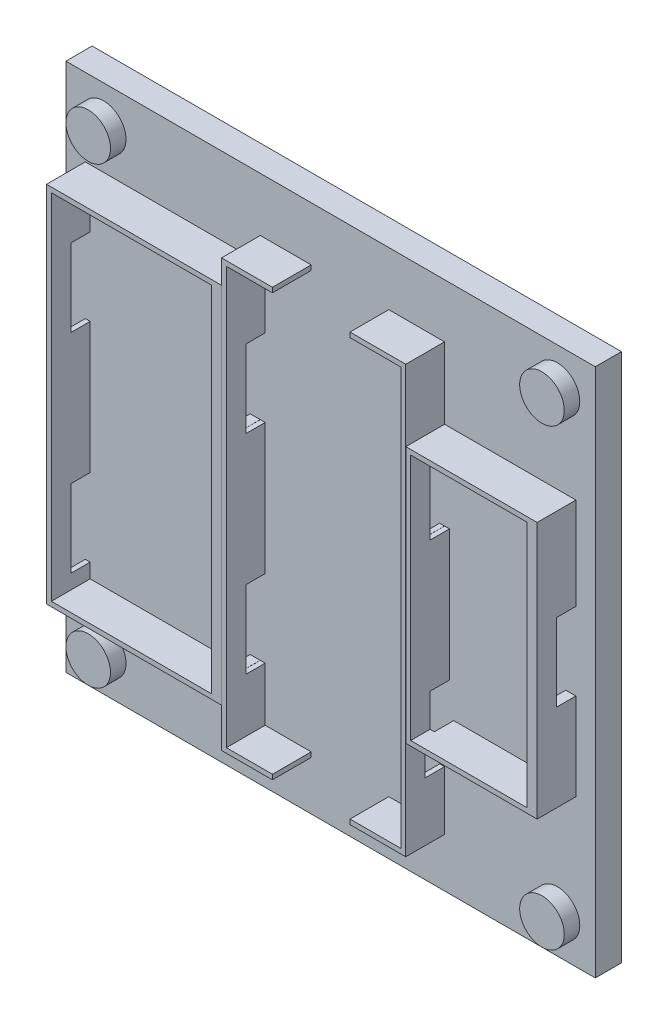
SolidWorks part; units mm, degrees
ref_plane "Přední rovina" through (0, 0, 0) normal (0, 0, 1) x (1, 0, 0)
ref_plane "Horní rovina" through (0, 0, 0) normal (0, 1, 0) x (1, 0, 0)
ref_plane "Pravá rovina" through (0, 0, 0) normal (1, 0, 0) x (0, 0, -1)
sketch "Skica1" plane through (0, 0, 0) normal (0, 0, 1) x (1, 0, 0)
  line L1 (-27.3, 27.3) -> (27.3, 27.3)
  line L2 (-27.3, 27.3) -> (-27.3, -27.3)
  line L3 (-27.3, -27.3) -> (27.3, -27.3)
  line L4 (27.3, 27.3) -> (27.3, -27.3)
  line L5 (-27.3, 27.3) -> (27.3, -27.3) construction
  line L6 (-27.3, -27.3) -> (27.3, 27.3) construction
  circle A0 centre (-23.4, 23.4) radius 2.3
  circle A1 centre (23.4, 23.4) radius 2.3
  circle A2 centre (-23.4, -23.4) radius 2.3
  circle A3 centre (23.4, -23.4) radius 2.3
  point P0 (0, 0)
  dimension "D2" = 4.6
  dimension "D6" = 4.6
  dimension "D9" = 4.6
  dimension "D11" = 4.6
  dimension "D1" = 54.6
  dimension "D3" = 3.9
  dimension "D4" = 3.9
  dimension "D5" = 5.5154
  dimension "D7" = 3.9
  dimension "D8" = 3.9
  dimension "D10" = 3.9
extrude "Přidat vysunutím1" add sketch "Skica1" along normal blind 1.7
sketch "Skica2" plane through (0, 0, 1.7) normal (0, 0, 1) x (1, 0, 0)
  line L1 (-27.3, 27.3) -> (27.3, 27.3)
  line L2 (-27.3, 27.3) -> (-27.3, -27.3)
  line L3 (-27.3, -27.3) -> (27.3, -27.3)
  line L4 (27.3, 27.3) -> (27.3, -27.3)
  line L5 (-27.3, 27.3) -> (27.3, -27.3) construction
  line L6 (-27.3, -27.3) -> (27.3, 27.3) construction
  point P0 (0, 0)
  dimension "D1" = 54.6
extrude "Přidat vysunutím2" add sketch "Skica2" along normal blind 1
sketch "Skica3" plane through (0, 0, 2.7) normal (0, 0, 1) x (1, 0, 0)
  line L0 (-27.3, 27.3) -> (-27.3, -27.3) construction
  line L1 (27.3, 27.3) -> (-27.3, 27.3) construction
  line L2 (27.3, -27.3) -> (27.3, 27.3) construction
  line L3 (-27.3, -27.3) -> (27.3, -27.3) construction
  circle A0 centre (-23.4, 23.4) radius 2.3
  circle A1 centre (23.4, 23.4) radius 2.3
  circle A2 centre (-23.4, -23.4) radius 2.3
  circle A3 centre (23.4, -23.4) radius 2.3
  dimension "D1" = 4.6
  dimension "D4" = 4.6
  dimension "D6" = 4.6
  dimension "D8" = 4.6
  dimension "D2" = 3.9
  dimension "D3" = 3.9
  dimension "D5" = 3.9
  dimension "D7" = 3.9
extrude "Přidat vysunutím3" add sketch "Skica3" along normal blind 1.6
sketch "Skica4" plane through (0, 0, 2.7) normal (0, 0, 1) x (1, 0, 0)
  line L0 (27.3, -27.3) -> (27.3, 27.3) construction
  line L1 (25.3, 14.3927) -> (11.76, 14.3927)
  line L2 (25.3, 14.3927) -> (25.3, -12.1073)
  line L3 (25.3, -12.1073) -> (11.76, -12.1073)
  line L4 (11.76, 14.3927) -> (11.76, -12.1073)
  line L5 (25.3, 14.3927) -> (11.76, -12.1073) construction
  line L6 (25.3, -12.1073) -> (11.76, 14.3927) construction
  line L7 (-27.3, 27.3) -> (-27.3, -27.3) construction
  line L8 (11.75, 21.75) -> (-7.25, 21.75)
  line L9 (11.75, 21.75) -> (11.75, -22.25)
  line L10 (11.75, -22.25) -> (-7.25, -22.25)
  line L11 (-7.25, 21.75) -> (-7.25, -22.25)
  line L12 (11.75, 21.75) -> (-7.25, -22.25) construction
  line L13 (11.75, -22.25) -> (-7.25, 21.75) construction
  line L14 (-7.26, 19.3) -> (-25.3, 19.3)
  line L15 (-7.26, 19.3) -> (-7.26, -18.2)
  line L16 (-7.26, -18.2) -> (-25.3, -18.2)
  line L17 (-25.3, 19.3) -> (-25.3, -18.2)
  line L18 (-7.26, 19.3) -> (-25.3, -18.2) construction
  line L19 (-7.26, -18.2) -> (-25.3, 19.3) construction
  line L20 (27.3, 27.3) -> (-27.3, 27.3) construction
  point P0 (18.53, 1.1427)
  point P7 (0, 0)
  point P12 (-16.28, 0.55)
  point P18 (0, 0)
  dimension "D1" = 26.5
  dimension "D2" = 13.54
  dimension "D3" = 2
  dimension "D4" = 44
  dimension "D5" = 19
  dimension "D6" = 37.5
  dimension "D7" = 18.04
  dimension "D8" = 0.01
  dimension "D9" = 2
  dimension "D10" = 0.01
  dimension "D11" = 8
extrude "Přidat vysunutím4" add sketch "Skica4" along normal blind 4
sketch "Skica5" plane through (0, -22.25, 0) normal (0, -1, 0) x (-1, 0, 0)
  line L0 (7.25, -6.7) -> (-11.75, -6.7) construction
  line L1 (-6, -6.7) -> (2, -6.7)
  line L2 (-6, -6.7) -> (-6, -2.7)
  line L3 (-6, -2.7) -> (2, -2.7)
  line L4 (2, -6.7) -> (2, -2.7)
  line L5 (27.3, -2.7) -> (-27.3, -2.7) construction
  line L8 (7.25, -6.7) -> (7.25, -2.7) construction
  line L9 (-11.75, -6.7) -> (-11.75, -2.7) construction
  dimension "D1" = 8
  dimension "D2" = 5.25
  dimension "D3" = 5.75
extrude "Odebrat vysunutím1" cut sketch "Skica5" against normal blind 6
sketch "Skica6" plane through (0, 21.75, 0) normal (0, 1, 0) x (1, 0, 0)
  line L0 (11.75, -6.7) -> (-7.25, -6.7) construction
  line L1 (-2, -2.7) -> (6, -2.7)
  line L2 (-2, -2.7) -> (-2, -6.7)
  line L3 (-2, -6.7) -> (6, -6.7)
  line L4 (6, -2.7) -> (6, -6.7)
  line L5 (-2, -2.7) -> (6, -6.7) construction
  line L6 (-2, -6.7) -> (6, -2.7) construction
  line L7 (-7.25, -6.7) -> (-7.25, -2.7) construction
  point P0 (2, -4.7)
  dimension "D1" = 4
  dimension "D2" = 8
  dimension "D3" = 0
  dimension "D4" = 5.25
extrude "Odebrat vysunutím2" cut sketch "Skica6" against normal blind 6
sketch "Skica7" plane through (-25.3, 0, 0) normal (-1, 0, 0) x (0, 0, 1)
  line L0 (2.7, -27.3) -> (2.7, 27.3) construction
  line L1 (2.7, -16.2) -> (4.7, -16.2)
  line L2 (2.7, -16.2) -> (2.7, -8.2)
  line L3 (2.7, -8.2) -> (4.7, -8.2)
  line L4 (4.7, -16.2) -> (4.7, -8.2)
  line L5 (2.7, -16.2) -> (4.7, -8.2) construction
  line L6 (2.7, -8.2) -> (4.7, -16.2) construction
  line L7 (6.7, -18.2) -> (2.7, -18.2) construction
  line L8 (2.7, 19.3) -> (2.7, -18.2) construction
  line L9 (2.7, 13.3) -> (4.7, 13.3)
  line L10 (2.7, 13.3) -> (2.7, 5.3)
  line L11 (2.7, 5.3) -> (4.7, 5.3)
  line L12 (4.7, 13.3) -> (4.7, 5.3)
  line L13 (6.7, 19.3) -> (2.7, 19.3) construction
  point P0 (3.7, -12.2)
  dimension "D1" = 8
  dimension "D2" = 2
  dimension "D3" = 0
  dimension "D4" = 2
  dimension "D5" = 8
  dimension "D6" = 2
  dimension "D7" = 6
extrude "Odebrat vysunutím3" cut sketch "Skica7" against normal blind 38
sketch "Skica8" plane through (25.3, 0, 0) normal (1, 0, 0) x (0, 0, -1)
  line L0 (-2.7, -12.1073) -> (-2.7, 14.3927) construction
  line L1 (-2.7, -3.1073) -> (-4.7, -3.1073)
  line L2 (-2.7, -3.1073) -> (-2.7, 4.8927)
  line L3 (-2.7, 4.8927) -> (-4.7, 4.8927)
  line L4 (-4.7, -3.1073) -> (-4.7, 4.8927)
  line L6 (-6.7, -12.1073) -> (-2.7, -12.1073) construction
  line L7 (-6.7, 14.3927) -> (-2.7, 14.3927) construction
  dimension "D1" = 8
  dimension "D2" = 2
  dimension "D3" = 9
  dimension "D4" = 9.5
extrude "Odebrat vysunutím4" cut sketch "Skica8" against normal blind 13
sketch "Skica11" plane through (0, 0, 6.7) normal (0, 0, 1) x (1, 0, 0)
  line L0 (-7.26, 19.3) -> (-25.3, 19.3) construction
  line L1 (-24.8, 18.8) -> (-8.3, 18.8)
  line L2 (-24.8, 18.8) -> (-24.8, -17.7)
  line L3 (-24.8, -17.7) -> (-8.3, -17.7)
  line L4 (-8.3, 18.8) -> (-8.3, -17.7)
  line L5 (-25.3, 19.3) -> (-25.3, -18.2) construction
  line L12 (-2, 21.75) -> (-7.25, 21.75) construction
  line L18 (-6.75, 21.25) -> (11.25, 21.25)
  line L19 (-6.75, 21.25) -> (-6.75, -21.75)
  line L20 (-6.75, -21.75) -> (11.25, -21.75)
  line L21 (11.25, 21.25) -> (11.25, -21.75)
  line L22 (11.75, -22.25) -> (11.75, 21.75) construction
  line L29 (11.76, 14.3927) -> (11.76, -12.1073) construction
  line L30 (12.26, 13.8927) -> (24.26, 13.8927)
  line L31 (12.26, 13.8927) -> (12.26, -11.6073)
  line L32 (12.26, -11.6073) -> (24.26, -11.6073)
  line L33 (24.26, 13.8927) -> (24.26, -11.6073)
  line L34 (25.3, 14.3927) -> (11.76, 14.3927) construction
  dimension "D1" = 36.5
  dimension "D2" = 16.5
  dimension "D3" = 0.5
  dimension "D4" = 0.5
  dimension "D5" = 43
  dimension "D6" = 18
  dimension "D7" = 0.5
  dimension "D8" = 0.5
  dimension "D9" = 25.5
  dimension "D10" = 12
  dimension "D11" = 0.5
  dimension "D12" = 0.5
extrude "Odebrat vysunutím5" cut sketch "Skica11" against normal blind 4
